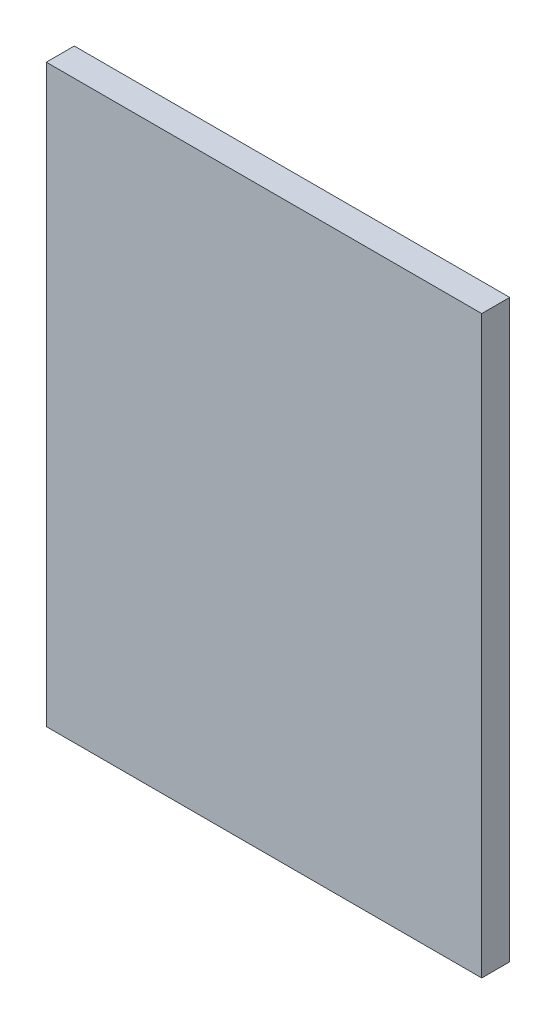
SolidWorks part; units mm, degrees
material "Balsa"
ref_plane "Front Plane" through (0, 0, 0) normal (0, 0, 1) x (1, 0, 0)
ref_plane "Top Plane" through (0, 0, 0) normal (0, 1, 0) x (1, 0, 0)
ref_plane "Right Plane" through (0, 0, 0) normal (1, 0, 0) x (0, 0, -1)
sketch "Sketch1" plane through (0, 0, 0) normal (0, 0, 1) x (1, 0, 0)
  line L1 (-140, 185) -> (140, 185)
  line L2 (-140, 185) -> (-140, -185)
  line L3 (-140, -185) -> (140, -185)
  line L4 (140, 185) -> (140, -185)
  line L5 (-140, 185) -> (140, -185) construction
  line L6 (-140, -185) -> (140, 185) construction
  point P0 (0, 0)
  dimension "D1" = 280
  dimension "D2" = 370
extrude "Boss-Extrude1" add sketch "Sketch1" along normal blind 18
